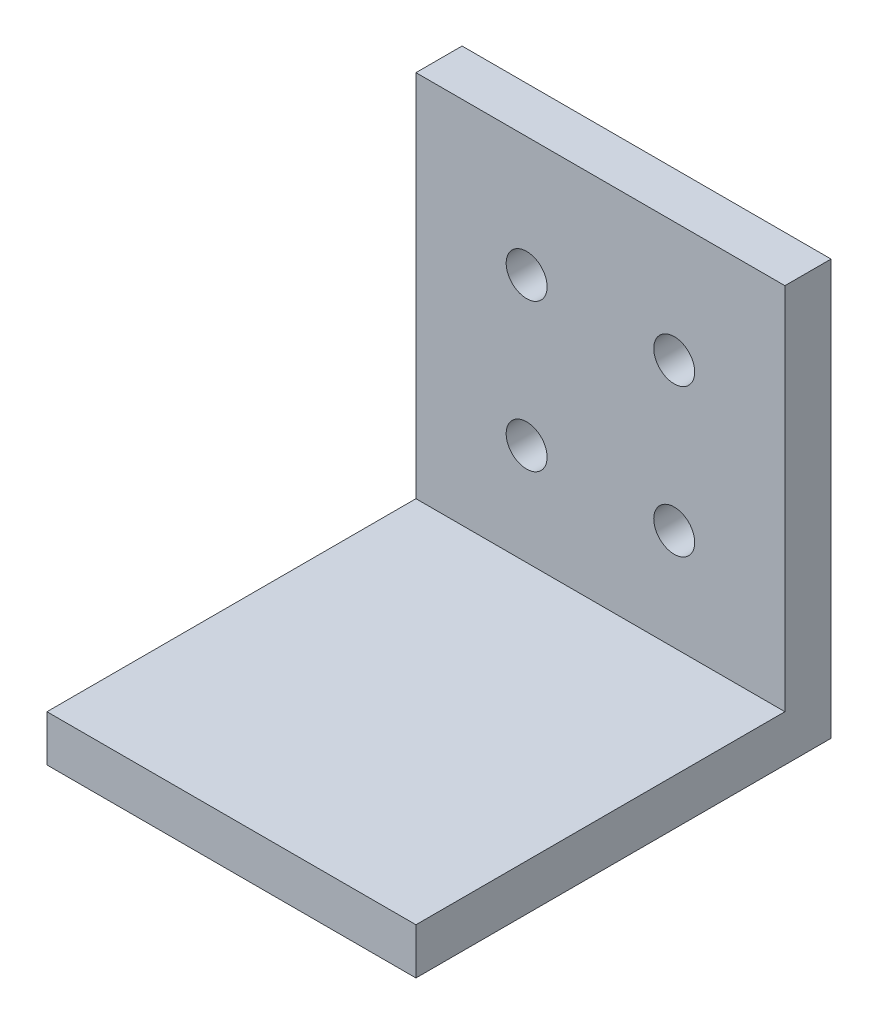
SolidWorks part; units mm, degrees
ref_plane "Front Plane" through (0, 0, 0) normal (0, 0, 1) x (1, 0, 0)
ref_plane "Top Plane" through (0, 0, 0) normal (0, 1, 0) x (1, 0, 0)
ref_plane "Right Plane" through (0, 0, 0) normal (1, 0, 0) x (0, 0, -1)
sketch "Sketch1" plane through (0, 0, 0) normal (0, 0, 1) x (1, 0, 0)
  line L1 (-12.7, 14.2875) -> (12.7, 14.2875)
  line L2 (-12.7, 14.2875) -> (-12.7, -14.2875)
  line L3 (-12.7, -14.2875) -> (12.7, -14.2875)
  line L4 (12.7, 14.2875) -> (12.7, -14.2875)
  line L5 (-12.7, 14.2875) -> (12.7, -14.2875) construction
  line L6 (-12.7, -14.2875) -> (12.7, 14.2875) construction
  point P0 (0, 0)
  dimension "D1" = 25.4
  dimension "D2" = 28.575
extrude "Boss-Extrude1" add sketch "Sketch1" along normal blind 3.175
sketch "Sketch2" plane through (0, 0, 3.175) normal (0, 0, 1) x (1, 0, 0)
  line L0 (12.7, -14.2875) -> (12.7, 14.2875) construction
  line L1 (-12.7, -14.2875) -> (12.7, -14.2875)
  line L2 (-12.7, -14.2875) -> (-12.7, -11.1125)
  line L3 (-12.7, -11.1125) -> (12.7, -11.1125)
  line L4 (12.7, -14.2875) -> (12.7, -11.1125)
  dimension "D1" = 3.175
extrude "Boss-Extrude2" add sketch "Sketch2" along normal blind 25.4
sketch "Sketch4" plane through (0, 0, 0) normal (0, 0, -1) x (-1, 0, 0)
  line L0 (-12.7, 14.2875) -> (12.7, 14.2875) construction
  line L1 (-12.7, -11.1125) -> (-12.7, 14.2875) construction
  circle A0 centre (-5.08, 6.0325) radius 1.4097
  dimension "D1" = 2.8194
  dimension "D2" = 8.255
  dimension "D3" = 7.62
extrude "Cut-Extrude1" cut sketch "Sketch4" against normal through all
pattern_linear "LPattern1" count 2 spacing 10.16 along (0, -1, 0) count 2 spacing 10.16 along (-1, 0, 0) of "Cut-Extrude1"
